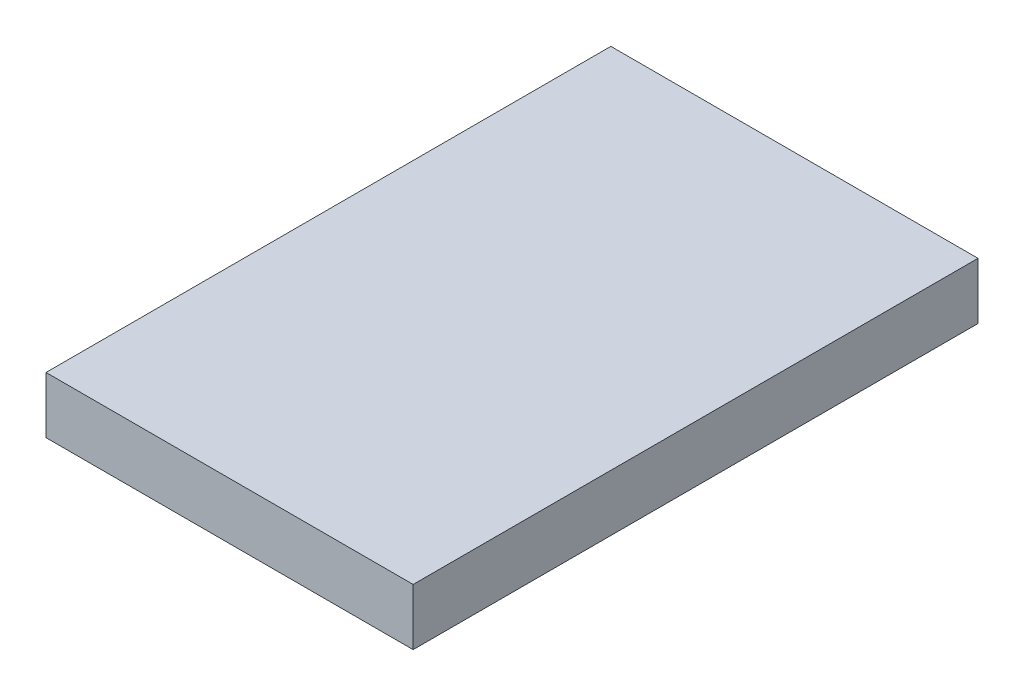
SolidWorks part; units mm, degrees
ref_plane "Front Plane" through (0, 0, 0) normal (0, 0, 1) x (1, 0, 0)
ref_plane "Top Plane" through (0, 0, 0) normal (0, 1, 0) x (1, 0, 0)
ref_plane "Right Plane" through (0, 0, 0) normal (1, 0, 0) x (0, 0, -1)
sketch "Sketch1" plane through (0, 0, 0) normal (0, 1, 0) x (1, 0, 0)
  line L1 (-13, -20) -> (13, -20)
  line L2 (-13, -20) -> (-13, 20)
  line L3 (-13, 20) -> (13, 20)
  line L4 (13, -20) -> (13, 20)
  line L5 (-13, -20) -> (13, 20) construction
  line L6 (-13, 20) -> (13, -20) construction
  point P1 (0, 0)
  dimension "D1" = 26
  dimension "D2" = 40
extrude "Boss-Extrude1" add sketch "Sketch1" along normal blind 4
sketch "Sketch2" plane through (0, 4, 0) normal (0, 1, 0) x (1, 0, 0)
  line L0 (-8, 20) -> (-8, -20) construction
  line L1 (13, 20) -> (-13, 20) construction
  line L2 (-13, -20) -> (13, -20) construction
  line L3 (-13, 20) -> (-13, -20) construction
  text T0 "ESC" font "Century Gothic" height in points 48
  dimension "D1" = 5
